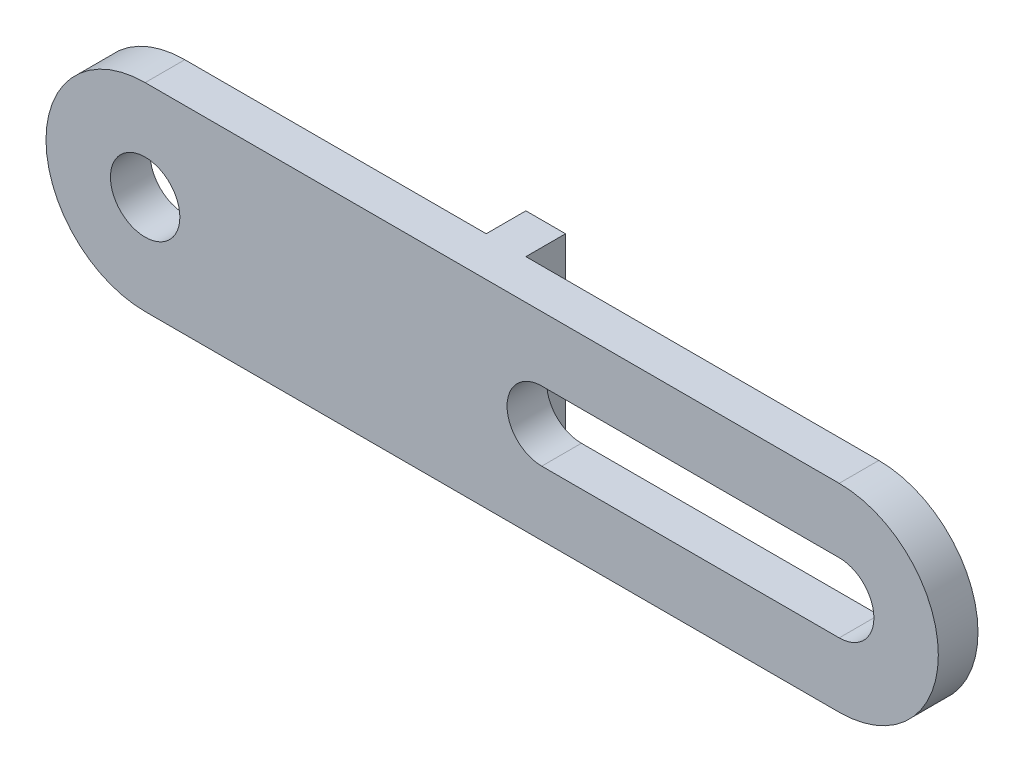
SolidWorks part; units mm, degrees
ref_plane "Plano frontal" through (0, 0, 0) normal (0, 0, 1) x (1, 0, 0)
ref_plane "Plano superior" through (0, 0, 0) normal (0, 1, 0) x (1, 0, 0)
ref_plane "Plano direito" through (0, 0, 0) normal (1, 0, 0) x (0, 0, -1)
sketch "Esboço1" plane through (0, 0, 0) normal (0, 0, 1) x (1, 0, 0)
  line L0 (0, 5) -> (35, 5)
  line L2 (35, -5) -> (0, -5)
  line L3 (20, 0) -> (35, 0) construction
  line L4 (20, 1.75) -> (35, 1.75)
  line L5 (20, -1.75) -> (35, -1.75)
  circle A0 centre (0, 0) radius 1.75
  arc A1 (0, 5) -> (0, -5) centre (0, 0) ccw
  arc A2 (20, 1.75) -> (20, -1.75) centre (20, 0) ccw
  arc A3 (35, -1.75) -> (35, 1.75) centre (35, 0) ccw
  arc A4 (35, 5) -> (35, -5) centre (35, 0) cw
  point P9 (27.5, 0)
  dimension "D1" = 3.5
  dimension "D2" = 5
  dimension "D4" = 15
  dimension "D3" = 35
extrude "Ressalto-extrusão1" add sketch "Esboço1" along normal blind 2
sketch "Esboço2" plane through (0, 0, 0) normal (0, 0, -1) x (-1, 0, 0)
  line L0 (-35, 5) -> (0, 5) construction
  line L1 (-15.2, 5) -> (-17.2, 5)
  line L2 (-15.2, 5) -> (-15.2, -5)
  line L3 (-15.2, -5) -> (-17.2, -5)
  line L4 (-17.2, 5) -> (-17.2, -5)
  line L6 (0, -5) -> (-35, -5) construction
  point P6 (-18.0974, -5)
  dimension "D1" = 15.2
  dimension "D2" = 2
extrude "Ressalto-extrusão2" add sketch "Esboço2" along normal blind 2
